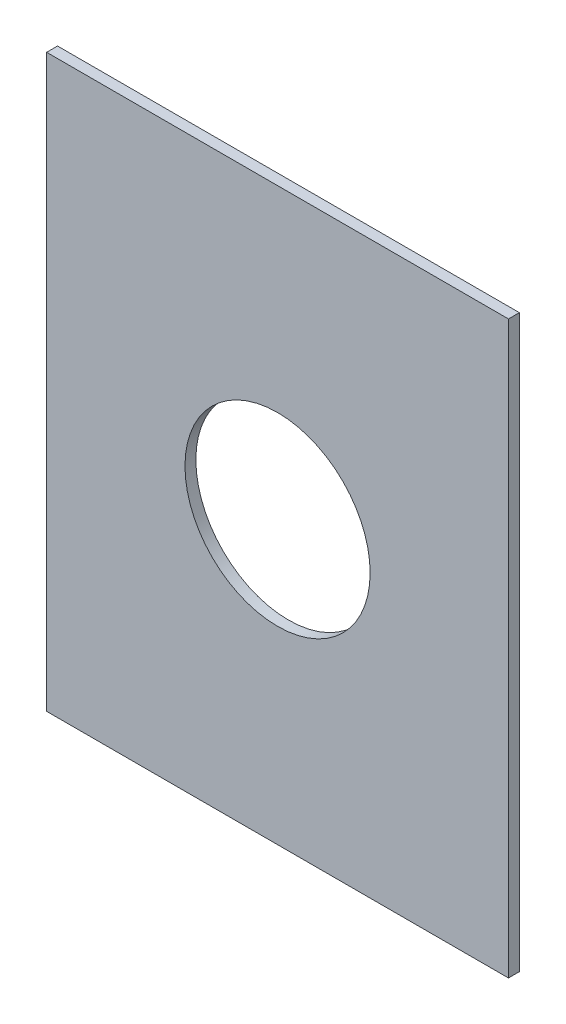
SolidWorks part; units mm, degrees
ref_plane "Plan de face" through (0, 0, 0) normal (0, 0, 1) x (1, 0, 0)
ref_plane "Plan de dessus" through (0, 0, 0) normal (0, 1, 0) x (1, 0, 0)
ref_plane "Plan de droite" through (0, 0, 0) normal (1, 0, 0) x (0, 0, -1)
sketch "Esquisse1" plane through (0, 0, 0) normal (0, 0, 1) x (1, 0, 0)
  line L1 (0, 0) -> (212, 0)
  line L2 (0, 0) -> (0, 262)
  line L3 (0, 262) -> (212, 262)
  line L4 (212, 0) -> (212, 262)
  dimension "D1" = 212
  dimension "D2" = 262
extrude "Boss.-Extru.1" add sketch "Esquisse1" along normal blind 5
sketch "Esquisse2" plane through (0, 0, 0) normal (0, 0, -1) x (-1, 0, 0)
  line L0 (-106, 262) -> (-106, 0) construction
  line L1 (-212, 262) -> (0, 262) construction
  line L2 (0, 0) -> (-212, 0) construction
  circle A0 centre (-106, 129.3) radius 42.5
  point P6 (-106, 129.3)
  dimension "D1" = 132.7
extrude "Enlèv. mat.-Extru.1" cut sketch "Esquisse2" against normal through all
